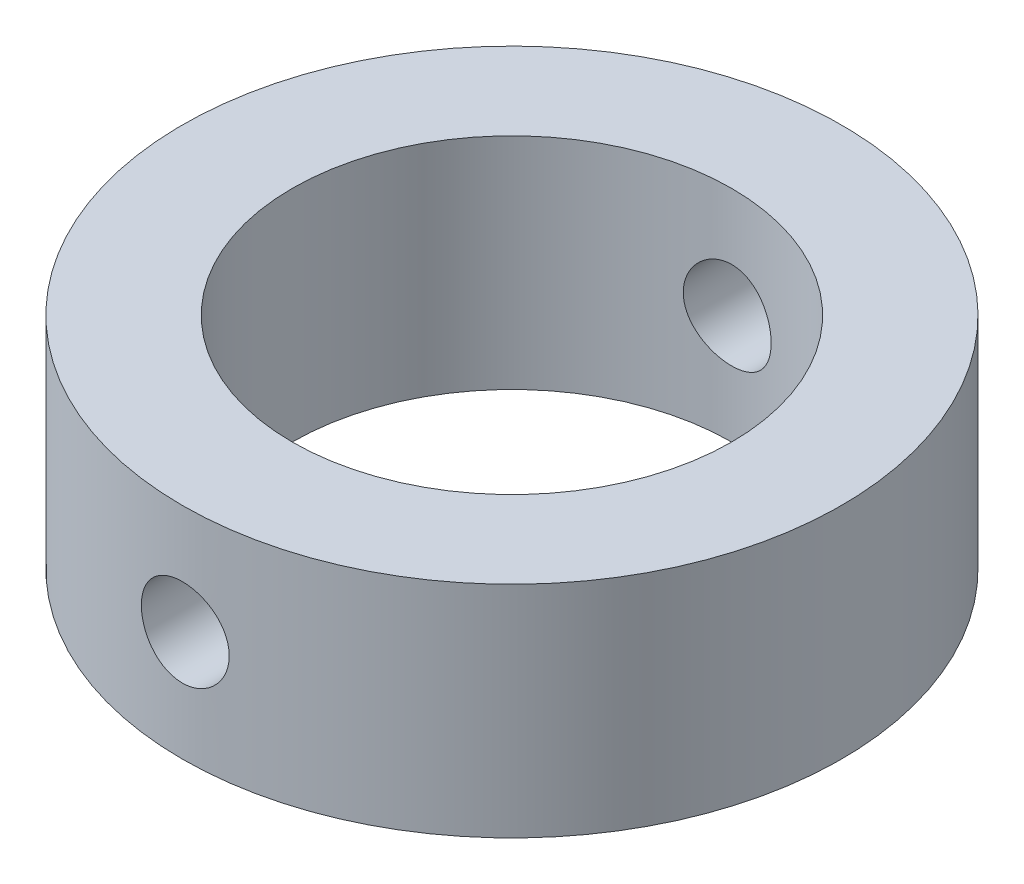
SolidWorks part; units mm, degrees
ref_plane "Front Plane" through (0, 0, 0) normal (0, 0, 1) x (1, 0, 0)
ref_plane "Top Plane" through (0, 0, 0) normal (0, 1, 0) x (1, 0, 0)
ref_plane "Right Plane" through (0, 0, 0) normal (1, 0, 0) x (0, 0, -1)
sketch "Sketch1" plane through (0, 0, 0) normal (0, 1, 0) x (1, 0, 0)
  circle A0 centre (0, 0) radius 15
  circle A1 centre (0, 0) radius 22.5
  dimension "D1" = 45
  dimension "D2" = 30
extrude "Boss-Extrude1" add sketch "Sketch1" along normal blind 15
sketch "Sketch2" plane through (0, 0, 0) normal (0, 0, 1) x (1, 0, 0)
  circle A0 centre (0, 7.5) radius 3
  dimension "D1" = 6
extrude "Cut-Extrude1" cut sketch "Sketch2" against normal mid plane 72
